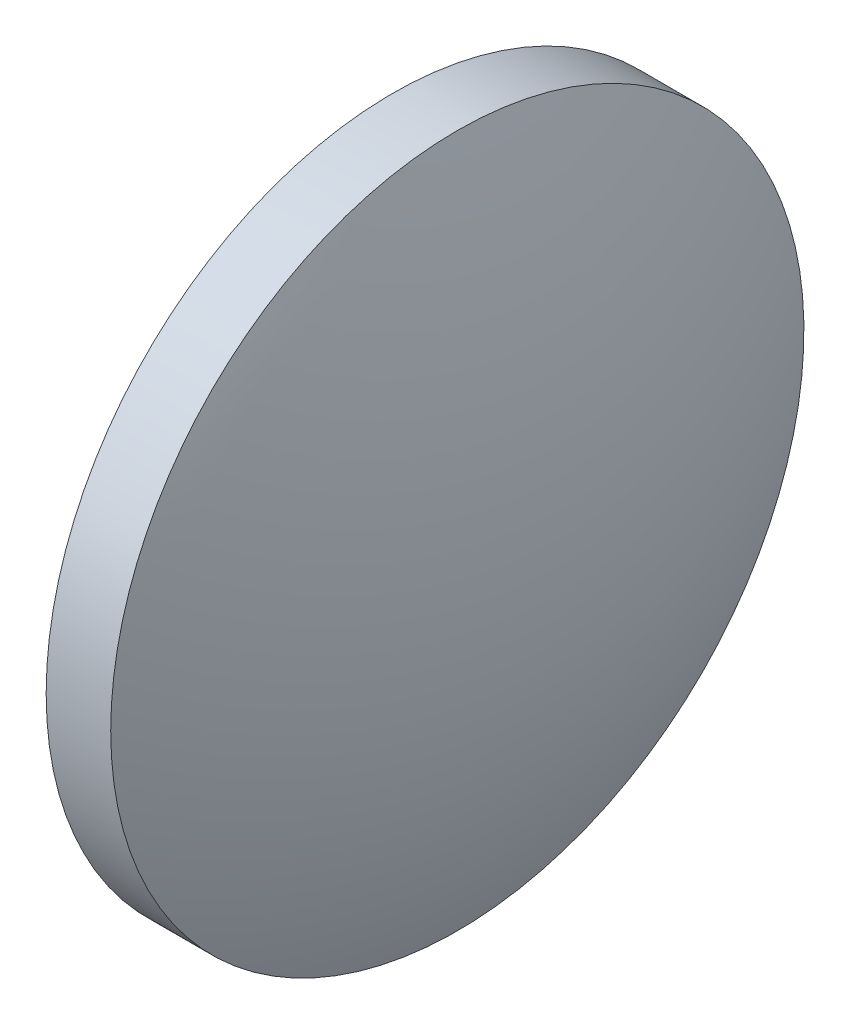
SolidWorks part; units mm, degrees
ref_plane "前视基准面" through (0, 0, 0) normal (0, 0, 1) x (1, 0, 0)
ref_plane "上视基准面" through (0, 0, 0) normal (0, 1, 0) x (1, 0, 0)
ref_plane "右视基准面" through (0, 0, 0) normal (1, 0, 0) x (0, 0, -1)
sketch "草图1" plane through (0, 0, 0) normal (0, 0, 1) x (1, 0, 0)
  line L0 (438.6233, 0.7682) -> (448.2191, 0.7682) construction
  line L1 (440.2713, 0.7682) -> (440.2713, 8.7682)
  line L2 (443.3713, 0.7682) -> (440.2713, 0.7682)
  line L5 (440.2713, 8.7682) -> (441.7613, 8.7682)
  arc A0 (443.3713, 0.7682) -> (441.7613, 8.7682) centre (422.6905, 0.7682) ccw
revolve "旋转1" add sketch "草图1" angle 360 about L0
